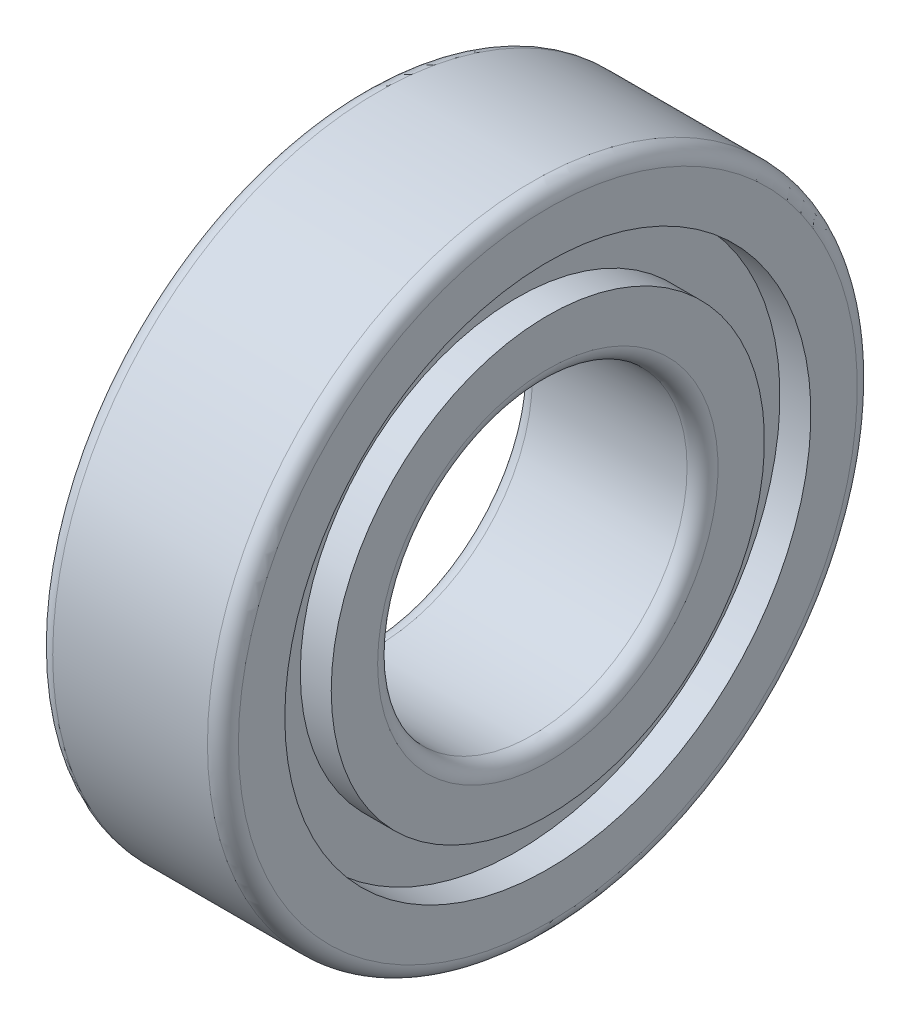
SolidWorks part; units mm, degrees
material "AISI 1020"
ref_plane "Спереди" through (0, 0, 0) normal (0, 0, 1) x (1, 0, 0)
ref_plane "Сверху" through (0, 0, 0) normal (0, 1, 0) x (1, 0, 0)
ref_plane "Справа" through (0, 0, 0) normal (1, 0, 0) x (0, 0, -1)
sketch "Эскиз1" plane through (0, 0, 0) normal (0, 0, 1) x (1, 0, 0)
  line L0 (-1000, 0) -> (49000, 0) construction
  line L1 (0, -1000) -> (0, 49000) construction
  line L2 (5, 10) -> (-5, 10)
  line L3 (-6, 11) -> (-6, 14)
  line L4 (-6, 14) -> (-4, 14)
  line L5 (-4, 14) -> (-4, 17)
  line L6 (-4, 17) -> (-6, 17)
  line L7 (-6, 17) -> (-6, 20)
  line L8 (-5, 21) -> (5, 21)
  line L9 (6, 17) -> (6, 20)
  line L10 (4, 17) -> (6, 17)
  line L11 (4, 14) -> (4, 17)
  line L12 (6, 14) -> (4, 14)
  line L13 (6, 11) -> (6, 14)
  arc A0 (-5, 10) -> (-6, 11) centre (-5, 11) cw
  arc A1 (-6, 20) -> (-5, 21) centre (-5, 20) cw
  arc A2 (6, 20) -> (5, 21) centre (5, 20) ccw
  arc A3 (5, 10) -> (6, 11) centre (5, 11) ccw
  point P23 (0, 21)
  point P27 (0, 10)
  dimension "_r" = 1
  dimension "_d" = 20
  dimension "D" = 42
  dimension "B" = 12
  dimension "D2" = 8
revolve "Повернуть1" add sketch "Эскиз1" angle 360 about L0
equation "\"D2@Эскиз1\"= \"B@Эскиз1\" / 3 * 2"
